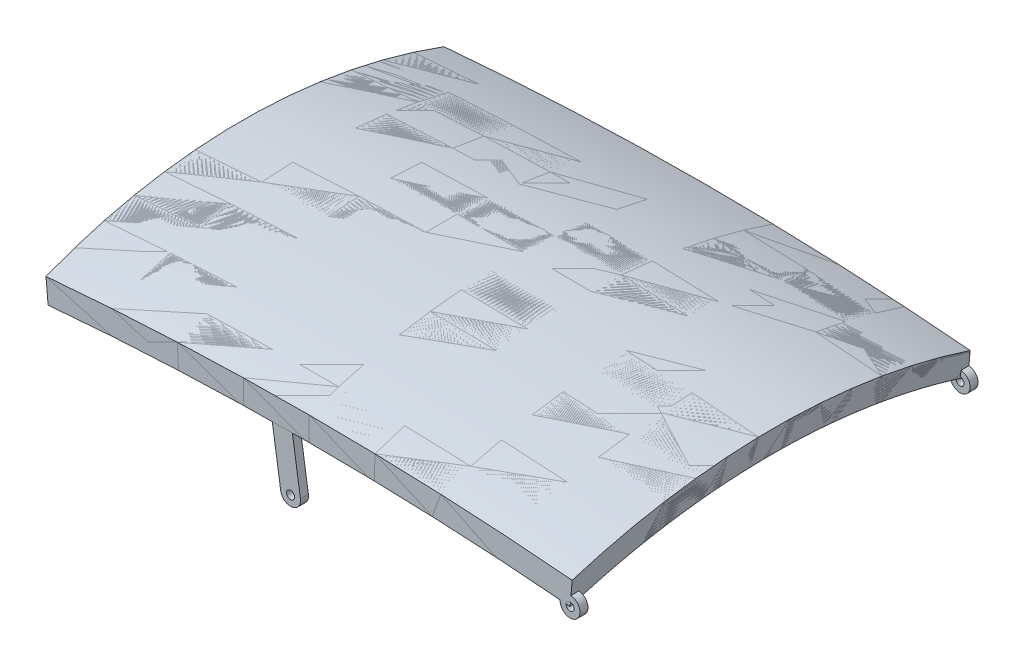
SolidWorks part; units mm, degrees
material "Alloy Steel"
ref_plane "Front Plane" through (0, 0, 0) normal (0, 0, 1) x (1, 0, 0)
ref_plane "Top Plane" through (0, 0, 0) normal (0, 1, 0) x (1, 0, 0)
ref_plane "Right Plane" through (0, 0, 0) normal (1, 0, 0) x (0, 0, -1)
sketch "Sketch1" plane through (0, 0, 0) normal (0, 0, 1) x (1, 0, 0)
  arc A0 (-381.3463, 0) -> (930.2537, 0) centre (274.4537, -7406.5232) cw
  dimension "D2" = 7435.5
  dimension "D1" = 1311.6
ref_plane "Plane1" through (-381.3463, 0, 0) normal (0.9961, 0.0882, 0) x (0, 0, -1)
sketch "Sketch2" plane through (-381.3463, 0, 0) normal (0.9961, 0.0882, 0) x (0, 0, -1)
  line L2 (1000, 0) -> (1000, 60)
  line L4 (0, 0) -> (0, 60)
  arc A0 (1000, 60) -> (0, 60) centre (500, -1354.2136) ccw
  arc A1 (1000, 0) -> (0, 0) centre (500, -1414.2136) ccw
  point P0 (0, 0)
  dimension "D3" = 1500
  dimension "D5" = 60
  dimension "D1" = 60
  dimension "D2" = 1000
  dimension "D4" = 60
sweep "Sweep1" add profiles "Sketch2" path "Sketch1"
sketch "Sketch3" plane through (0, 0, 0) normal (0, 0, 1) x (1, 0, 0)
  line L0 (-381.3463, 0) -> (930.2537, 0) construction
  line L1 (207.1537, 28.6722) -> (227.9709, -108.3278)
  line L2 (203.2546, -112.0835) -> (181.908, 28.4008)
  line L3 (252.6872, -104.5722) -> (232.4125, 28.8579)
  line L5 (179.8889, 41.689) -> (230.4628, 41.689)
  line L6 (232.4125, 28.8579) -> (230.4628, 41.689)
  line L7 (207.1537, 28.6722) -> (205.1758, 41.689)
  line L8 (181.908, 28.4008) -> (179.8889, 41.689)
  arc A0 (930.2537, 0) -> (-381.3463, 0) centre (274.4537, -7406.5232) ccw construction
  circle A1 centre (227.9709, -108.3278) radius 10
  circle A2 centre (227.9709, -108.3278) radius 25
  point P15 (231.2613, 42.6645)
  point P18 (179.8889, 41.689)
  dimension "D4" = 20
  dimension "D5" = 50
  dimension "D1" = 81.36
  dimension "D2" = 137
  dimension "D3" = 723.1
extrude "Boss-Extrude1" add sketch "Sketch3" against normal blind 20 separate body
sketch "Sketch4" plane through (0, 0, 0) normal (0, 0, 1) x (1, 0, 0)
  circle A1 centre (930.2537, 0) radius 25
  dimension "D2" = 50
extrude "Boss-Extrude2" add sketch "Sketch4" against normal blind 20
sketch "Sketch5" plane through (0, 0, 0) normal (0, 0, 1) x (1, 0, 0)
  circle A0 centre (930.2537, 0) radius 10
  dimension "D1" = 20
extrude "Cut-Extrude1" cut sketch "Sketch5" against normal blind 40
sketch "Sketch8" plane through (-378.3798, -33.5031, 0) normal (-0.9961, -0.0882, 0) x (0, 0, 1)
  line L0 (0, 33.6342) -> (-1000, 33.6342)
ref_point "Point1"
ref_plane "Plane2" through (0, 0, -500) normal (0, 0, 1) x (1, 0, 0)
mirror "Mirror5" about plane through (0, 0, -500) normal (0, 0, 1) of bodies 102 104
